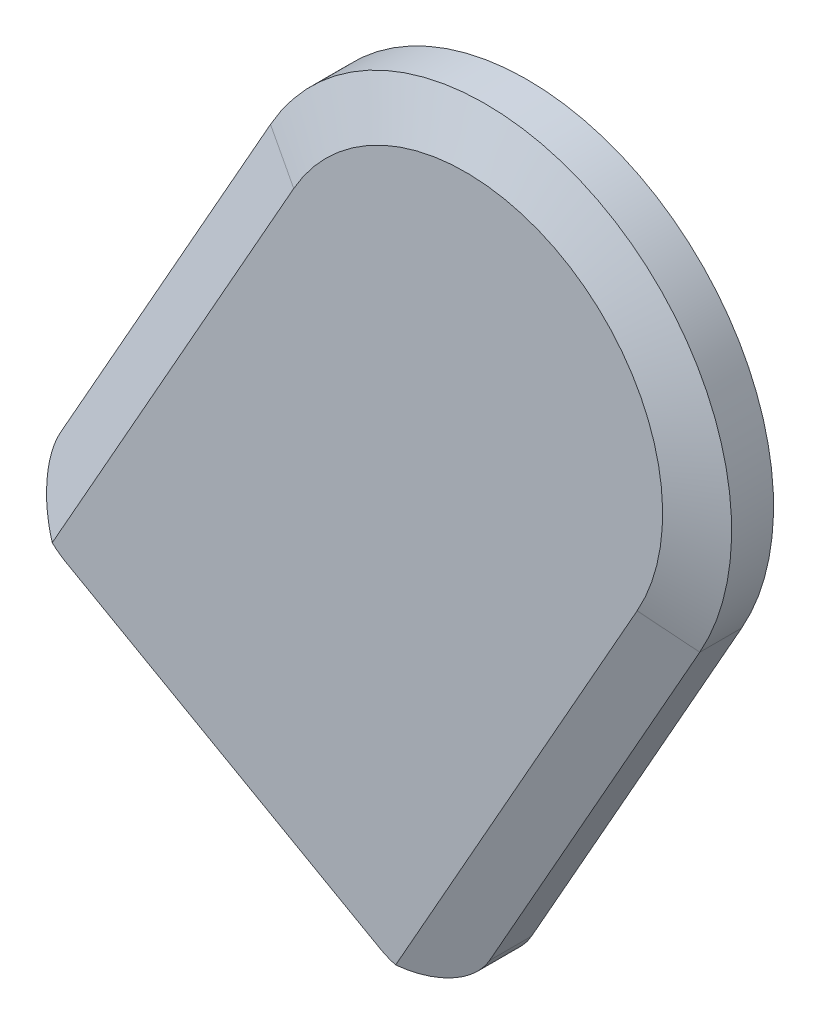
SolidWorks part; units mm, degrees
ref_plane "Front Plane" through (0, 0, 0) normal (0, 0, 1) x (1, 0, 0)
ref_plane "Top Plane" through (0, 0, 0) normal (0, 1, 0) x (1, 0, 0)
ref_plane "Right Plane" through (0, 0, 0) normal (1, 0, 0) x (0, 0, -1)
sketch "Sketch1" plane through (0, 0, 0) normal (0, 0, 1) x (1, 0, 0)
  line L0 (-16.5861, 9.3704) -> (-35.3269, -23.8018)
  line L1 (16.5861, -9.3704) -> (-2.1547, -42.5426)
  line L2 (-35.3269, -23.8018) -> (-2.1547, -42.5426)
  arc A0 (16.5861, -9.3704) -> (-16.5861, 9.3704) centre (0, 0) ccw
  dimension "D1" = 38.1
  dimension "D2" = 90
  dimension "D3" = 38.1
extrude "Boss-Extrude1" add sketch "Sketch1" along normal blind 4.7625
chamfer "Chamfer1" distance 1.524 distance2 3.81 3 edges at (7.2157, -25.9565, 4.7625) (-25.9565, -7.2157, 4.7625) (9.3704, 16.5861, 4.7625)
fillet "Fillet1" radius 5.08 2 edges at (-35.3269, -23.8018, 1.6193) (-2.1547, -42.5426, 1.6193)
